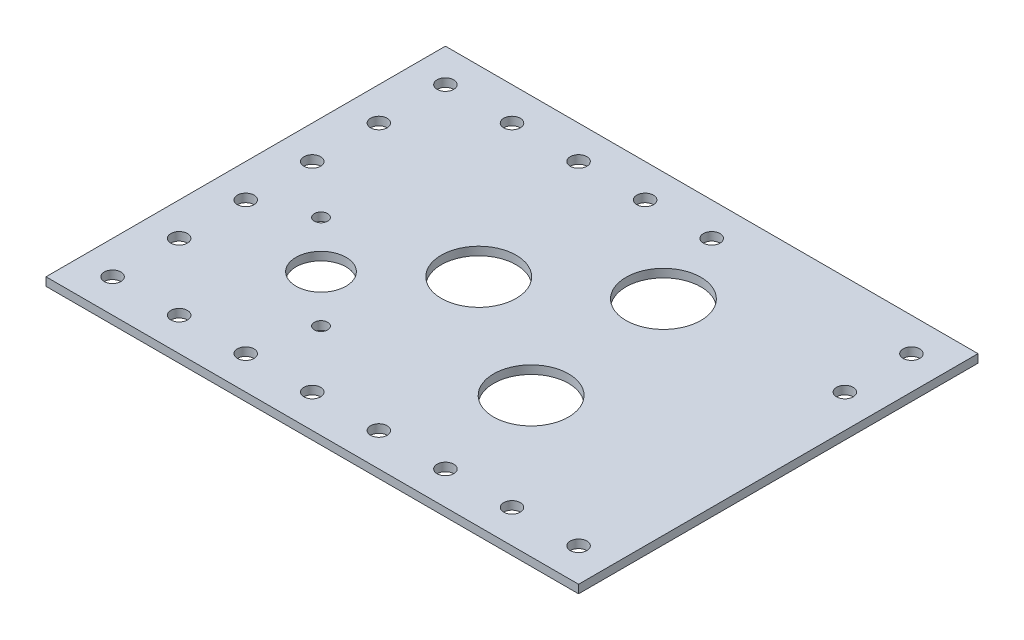
SolidWorks part; units mm, degrees
material "6061 Alloy"
ref_plane "Front Plane" through (0, 0, 0) normal (0, 0, 1) x (1, 0, 0)
ref_plane "Top Plane" through (0, 0, 0) normal (0, 1, 0) x (1, 0, 0)
ref_plane "Right Plane" through (0, 0, 0) normal (1, 0, 0) x (0, 0, -1)
sketch "Sketch1" plane through (0, 0, 0) normal (0, 1, 0) x (1, 0, 0)
  line L1 (0, 0) -> (203.2, 0)
  line L2 (0, 0) -> (0, 152.4)
  line L3 (0, 152.4) -> (203.2, 152.4)
  line L4 (203.2, 0) -> (203.2, 152.4)
extrude "Boss-Extrude1" add sketch "Sketch1" along normal blind 3.175
sketch "Sketch4" plane through (0, 3.175, 0) normal (0, 1, 0) x (1, 0, 0)
  circle A0 centre (12.7, 12.7) radius 3.175
  circle A2 centre (38.1, 12.7) radius 3.175
  circle A4 centre (63.5, 12.7) radius 3.175
  circle A6 centre (88.9, 12.7) radius 3.175
  circle A8 centre (114.3, 12.7) radius 3.175
  circle A10 centre (139.7, 12.7) radius 3.175
  circle A12 centre (165.1, 12.7) radius 3.175
  circle A14 centre (190.5, 12.7) radius 3.175
  circle A16 centre (12.7, 38.1) radius 3.175
  circle A18 centre (12.7, 63.5) radius 3.175
  circle A20 centre (12.7, 88.9) radius 3.175
  circle A22 centre (12.7, 114.3) radius 3.175
  circle A24 centre (12.7, 139.7) radius 3.175
  circle A26 centre (38.1, 139.7) radius 3.175
  circle A28 centre (63.5, 139.7) radius 3.175
  circle A30 centre (88.9, 139.7) radius 3.175
  circle A32 centre (114.3, 139.7) radius 3.175
  circle A41 centre (190.5, 114.3) radius 3.175
  circle A43 centre (190.5, 139.7) radius 3.175
  circle A44 centre (190.5, 127) radius 3.175 [skipped]
  circle A45 centre (190.5, 101.6) radius 3.175 [skipped]
  circle A46 centre (190.5, 88.9) radius 3.175 [skipped]
  circle A47 centre (190.5, 76.2) radius 3.175 [skipped]
  circle A48 centre (190.5, 63.5) radius 3.175 [skipped]
  circle A49 centre (190.5, 50.8) radius 3.175 [skipped]
  circle A50 centre (190.5, 38.1) radius 3.175 [skipped]
  circle A51 centre (190.5, 25.4) radius 3.175 [skipped]
  circle A52 centre (177.8, 12.7) radius 3.175 [skipped]
  circle A53 centre (152.4, 12.7) radius 3.175 [skipped]
  circle A54 centre (127, 12.7) radius 3.175 [skipped]
  circle A55 centre (101.6, 12.7) radius 3.175 [skipped]
  circle A56 centre (76.2, 12.7) radius 3.175 [skipped]
  circle A57 centre (50.8, 12.7) radius 3.175 [skipped]
  circle A58 centre (25.4, 12.7) radius 3.175 [skipped]
  circle A59 centre (12.7, 127) radius 3.175 [skipped]
  circle A60 centre (12.7, 101.6) radius 3.175 [skipped]
  circle A61 centre (12.7, 76.2) radius 3.175 [skipped]
  circle A62 centre (12.7, 50.8) radius 3.175 [skipped]
  circle A63 centre (12.7, 25.4) radius 3.175 [skipped]
  circle A64 centre (25.4, 139.7) radius 3.175 [skipped]
  circle A65 centre (50.8, 139.7) radius 3.175 [skipped]
  circle A66 centre (76.2, 139.7) radius 3.175 [skipped]
  circle A67 centre (101.6, 139.7) radius 3.175 [skipped]
  circle A68 centre (127, 139.7) radius 3.175 [skipped]
  dimension "D1" = 15
  dimension "D2" = 11
  dimension "D3" = 10
  dimension "D4" = 11
sketch "Sketch5" plane through (0, 3.175, 0) normal (0, 1, 0) x (1, 0, 0)
  circle A0 centre (50.8, 54.1274) radius 9.5504
  circle A1 centre (32.8422, 72.0852) radius 2.54
  circle A2 centre (68.7578, 36.1696) radius 2.54
extrude "Cut-Extrude4" cut sketch "Sketch5" against normal blind 4.7625
sketch "Sketch6" plane through (0, 3.175, 0) normal (0, 1, 0) x (1, 0, 0)
  circle A0 centre (82.55, 82.55) radius 14.29
extrude "Cut-Extrude5" cut sketch "Sketch6" against normal blind 4.7625
sketch "Sketch7" plane through (0, 3.175, 0) normal (0, 1, 0) x (1, 0, 0)
  circle A0 centre (125.095, 110.49) radius 14.2875
  circle A1 centre (131.7498, 53.34) radius 14.2875
extrude "Cut-Extrude7" cut sketch "Sketch4" against normal blind 5.08
extrude "Cut-Extrude8" cut sketch "Sketch7" against normal blind 25.4
